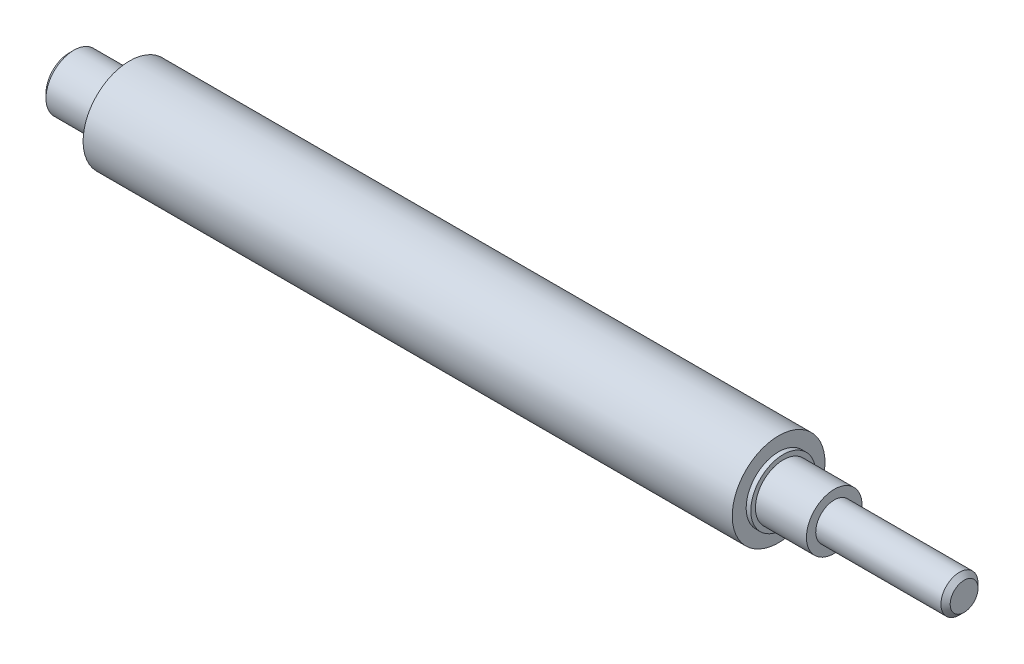
SolidWorks part; units mm, degrees
material "Brass"
ref_plane "Front Plane" through (0, 0, 0) normal (0, 0, 1) x (1, 0, 0)
ref_plane "Top Plane" through (0, 0, 0) normal (0, 1, 0) x (1, 0, 0)
ref_plane "Right Plane" through (0, 0, 0) normal (1, 0, 0) x (0, 0, -1)
sketch "Sketch1" plane through (0, 0, 0) normal (0, 0, 1) x (1, 0, 0)
  line L0 (0, 0) -> (0, 3)
  line L1 (0, 3) -> (6, 3)
  line L2 (6.5, 3.5) -> (6.5, 5)
  line L3 (6.5, 5) -> (76.5, 5)
  line L4 (76.5, 5) -> (76.5, 3.5)
  line L5 (77, 3) -> (82.5, 3)
  line L6 (82.5, 3) -> (82.5, 2)
  line L7 (82.5, 2) -> (96.5, 2)
  line L8 (96.5, 2) -> (96.5, 0)
  line L9 (96.5, 0) -> (0, 0)
  line L10 (76.5, 3.5) -> (77, 3.5)
  line L11 (77, 3.5) -> (77, 3)
  line L12 (6, 3) -> (6, 3.5)
  line L13 (6, 3.5) -> (6.5, 3.5)
  dimension "D1" = 3
  dimension "D2" = 5
  dimension "D3" = 71
  dimension "D4" = 0.5
  dimension "D5" = 20
  dimension "D6" = 6
  dimension "D7" = 2
  dimension "D8" = 6
revolve "Revolve1" add sketch "Sketch1" angle 360 about L9
chamfer "Chamfer1" distance 0.5 angle 45 2 edges at (0, 3, 0) (96.5, 2, 0)
